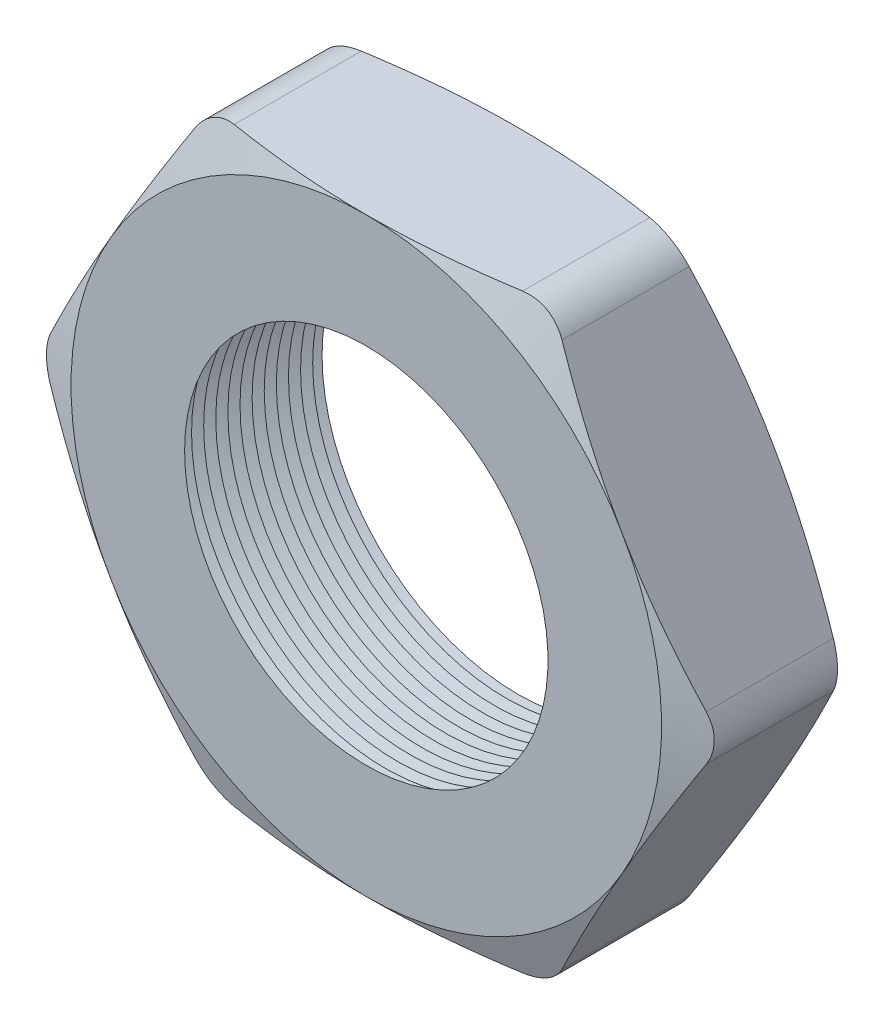
SolidWorks part; units mm, degrees
ref_plane "Front Plane" through (0, 0, 0) normal (0, 0, 1) x (1, 0, 0)
ref_plane "Top Plane" through (0, 0, 0) normal (0, 1, 0) x (1, 0, 0)
ref_plane "Right Plane" through (0, 0, 0) normal (1, 0, 0) x (0, 0, -1)
sketch "Sketch1" plane through (0, 0, 0) normal (0, 0, 1) x (1, 0, 0)
  line L1 (-5.7192, 0) -> (-2.8596, -4.953)
  line L2 (-2.8596, -4.953) -> (2.8596, -4.953)
  line L3 (2.8596, -4.953) -> (5.7192, 0)
  line L4 (5.7192, 0) -> (2.8596, 4.953)
  line L5 (2.8596, 4.953) -> (-2.8596, 4.953)
  line L6 (-2.8596, 4.953) -> (-5.7192, 0)
  circle A0 centre (0, 0) radius 4.953 construction
  circle A1 centre (0, 0) radius 3.048
  dimension "TS" = 6.096
  dimension "H" = 9.906
extrude "Extrude1" add sketch "Sketch1" along normal blind 2.54
fillet "Fillet1" radius 0.762 6 edges at (-2.8596, 4.953, 1.27) (-5.7192, 0, 1.27) (-2.8596, -4.953, 1.27) (2.8596, -4.953, 1.27) (5.7192, 0, 1.27) (2.8596, 4.953, 1.27)
sketch "Sketch2" plane through (0, 0, 2.54) normal (0, 0, 1) x (1, 0, 0)
  line L0 (2.4197, 4.953) -> (-2.4197, 4.953) construction
  circle A0 centre (0, 0) radius 4.953
extrude "Cut-Extrude1" cut sketch "Sketch2" against normal through all draft 70 flip side to cut
sketch "Sketch3" plane through (0, 0, 0) normal (0, 0, -1) x (-1, 0, 0)
  circle A0 centre (0, 0) radius 4.953
extrude "Cut-Extrude2" cut sketch "Sketch3" against normal through all draft 70 flip side to cut
sketch "Sketch4" plane through (0, 0, 0) normal (0, 1, 0) x (1, 0, 0)
  line L0 (-3.048, -2.54) -> (-3.048, -2.1001)
  line L2 (-3.048, -2.1001) -> (-3.429, -2.32)
  line L3 (-3.429, -2.32) -> (-3.048, -2.54)
  line L5 (-3.048, 0) -> (-3.048, -2.54) construction
  line L6 (-3.048, -2.54) -> (3.048, -2.54) construction
  dimension "D1" = 60
  dimension "D2" = 60
  dimension "D3" = 0.381
revolve "Cut-Revolve1" cut sketch "Sketch4" angle 360 about axis through (0, 0, 2.54) along (0, 0, -1)
pattern_linear "LPattern1" count 13 spacing 0.2032 along (0, 0, -1) of "Cut-Revolve1"
